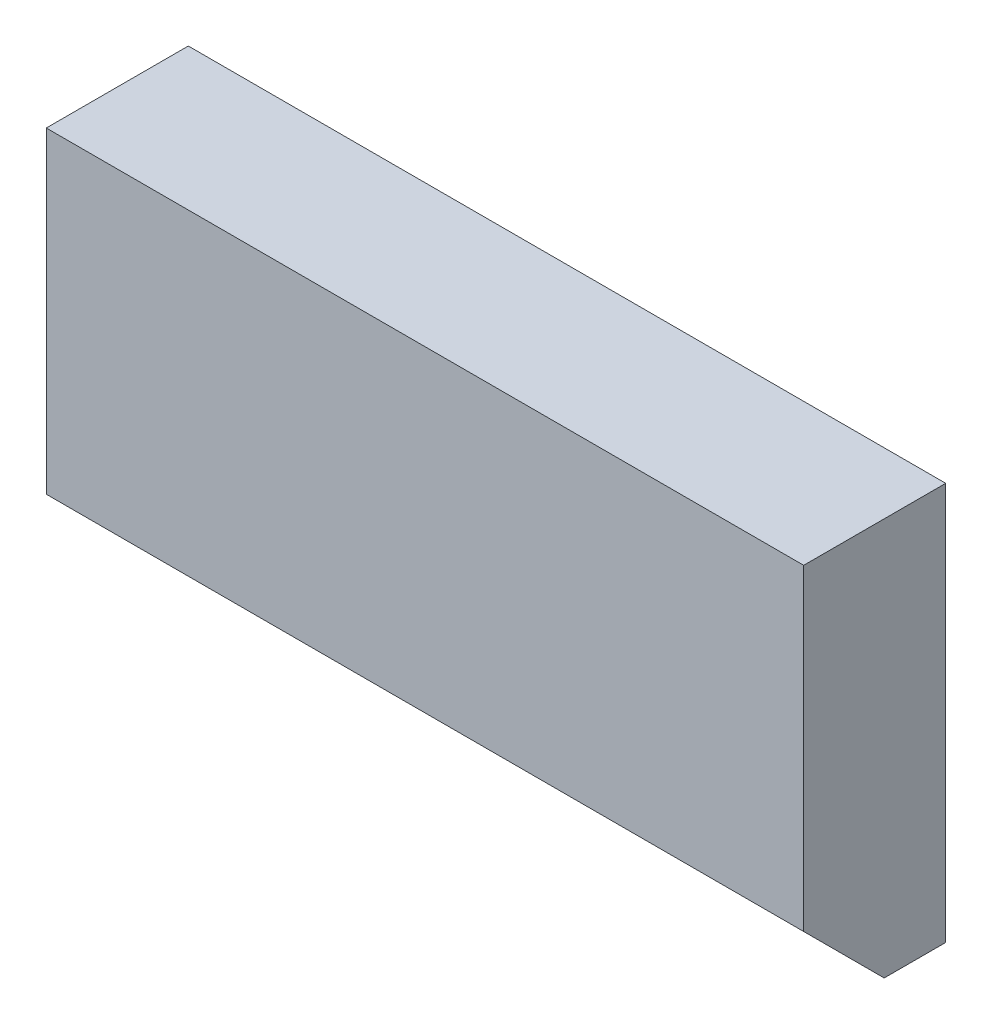
SolidWorks part; units mm, degrees
material "Стекло"
ref_plane "Спереди" through (0, 0, 0) normal (0, 0, 1) x (1, 0, 0)
ref_plane "Сверху" through (0, 0, 0) normal (0, 1, 0) x (1, 0, 0)
ref_plane "Справа" through (0, 0, 0) normal (1, 0, 0) x (0, 0, -1)
sketch "Эскиз1" plane through (0, 0, 0) normal (0, 0, 1) x (1, 0, 0)
  line L1 (16, 0) -> (0, 0)
  line L2 (16, 0) -> (16, 8.7)
  line L3 (16, 8.7) -> (0, 8.7)
  line L4 (0, 0) -> (0, 8.7)
  dimension "D1" = 8.7
  dimension "D2" = 16
extrude "Вытянуть1" add sketch "Эскиз1" along normal blind 3
chamfer "Фаска3" distance 2 angle 45 1 edges at (8, 0, 3)
chamfer "Фаска1" [suppressed] distance 0.3 angle 45
ref_point "Точка1"
chamfer "Фаска4" distance 0.3 angle 45 1 edges at (16, 0, 0.5)
